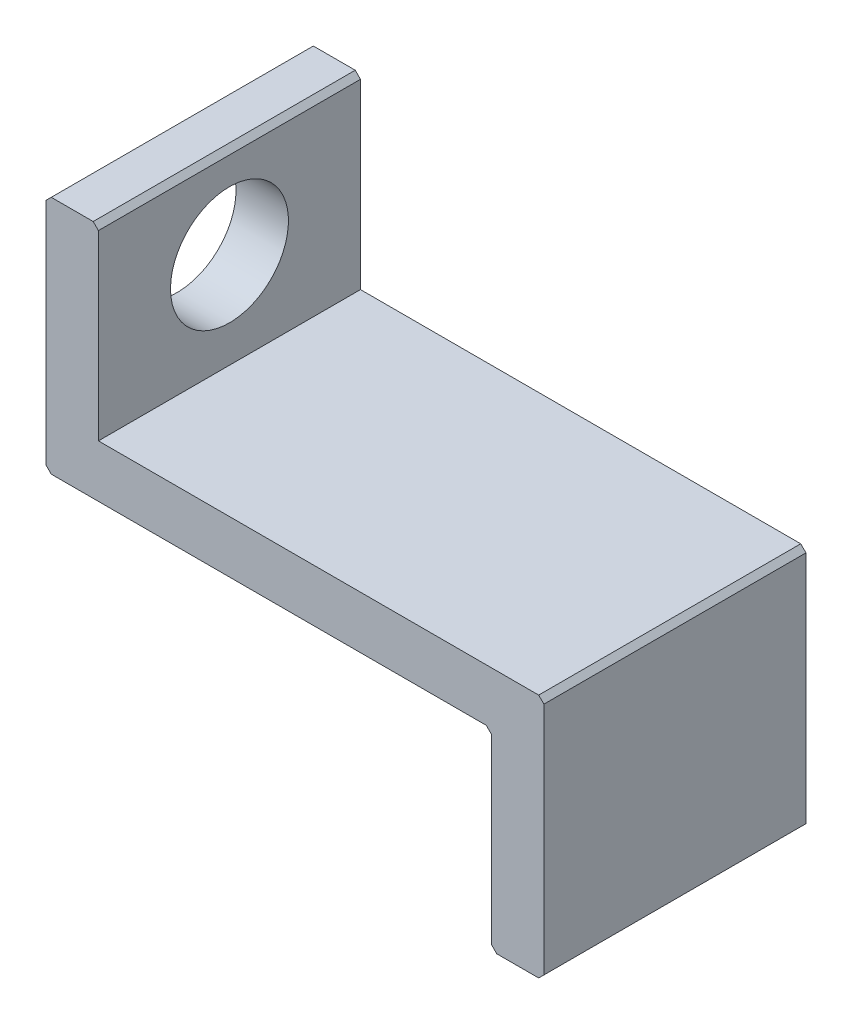
SolidWorks part; units mm, degrees
ref_plane "Plan de face" through (0, 0, 0) normal (0, 0, 1) x (1, 0, 0)
ref_plane "Plan de dessus" through (0, 0, 0) normal (0, 1, 0) x (1, 0, 0)
ref_plane "Plan de droite" through (0, 0, 0) normal (1, 0, 0) x (0, 0, -1)
sketch "Esquisse1" plane through (0, 0, 0) normal (0, 0, 1) x (1, 0, 0)
  line L0 (-90.244, 0) -> (109.319, 0) construction
  line L1 (0, 32) -> (0, 41.35)
  line L2 (0, 41.35) -> (-17, 41.35)
  line L3 (-17, 41.35) -> (-17, 48.5)
  line L4 (-17, 48.5) -> (-19, 48.5)
  line L5 (-19, 48.5) -> (-19, 39.35)
  line L6 (-19, 39.35) -> (-2, 39.35)
  line L7 (-2, 39.35) -> (-2, 32)
  line L8 (-2, 32) -> (0, 32)
  dimension "D1" = 64
  dimension "D2" = 78.7
  dimension "D3" = 97
  dimension "D4" = 2
  dimension "D5" = 2
  dimension "D6" = 2
  dimension "D7" = 17
extrude "Boss.-Extru.1" add sketch "Esquisse1" along normal blind 10 contours L4 L5 L6 L7 L8 L1 L2 L3
chamfer "Chanfrein2" distance 0.2 angle 45 7 edges at (-19, 48.5, 5) (-19, 39.35, 5) (-2, 39.35, 5) (-17, 48.5, 5) (0, 41.35, 5) (-2, 32, 5) (0, 32, 5)
hole_wizard "Dégagement M41" positions "Esquisse2" profile "Esquisse4" hole size "M4" standard "ISO" end condition through all
sketch "Esquisse2" plane through (-19, 0, 0) normal (-1, 0, 0) x (0, 0, 1)
  line L0 (0, 0) -> (41.5026, 0) construction
  line L2 (5, 45) -> (5, 0) construction
  line L3 (0, 0) -> (0, -2.831) construction
  point P0 (5, 45)
  dimension "D1" = 45
  dimension "D2" = 5
sketch "Esquisse4" plane through (-19, 45, 5) normal (0, 1, 0) x (0, 0, 1)
  line L0 (0, 0) -> (0, 19)
  line L1 (0, 19) -> (2.25, 19)
  line L2 (2.25, 19) -> (2.25, 0)
  line L5 (2.25, 0) -> (0, 0)
  line L11 (0, -6.35) -> (0, 107.95) construction
  dimension "Diamètre du perçage jusqu'au prochain" = 4.5
  dimension "Profondeur du perçage jusqu'au prochain" = 19
